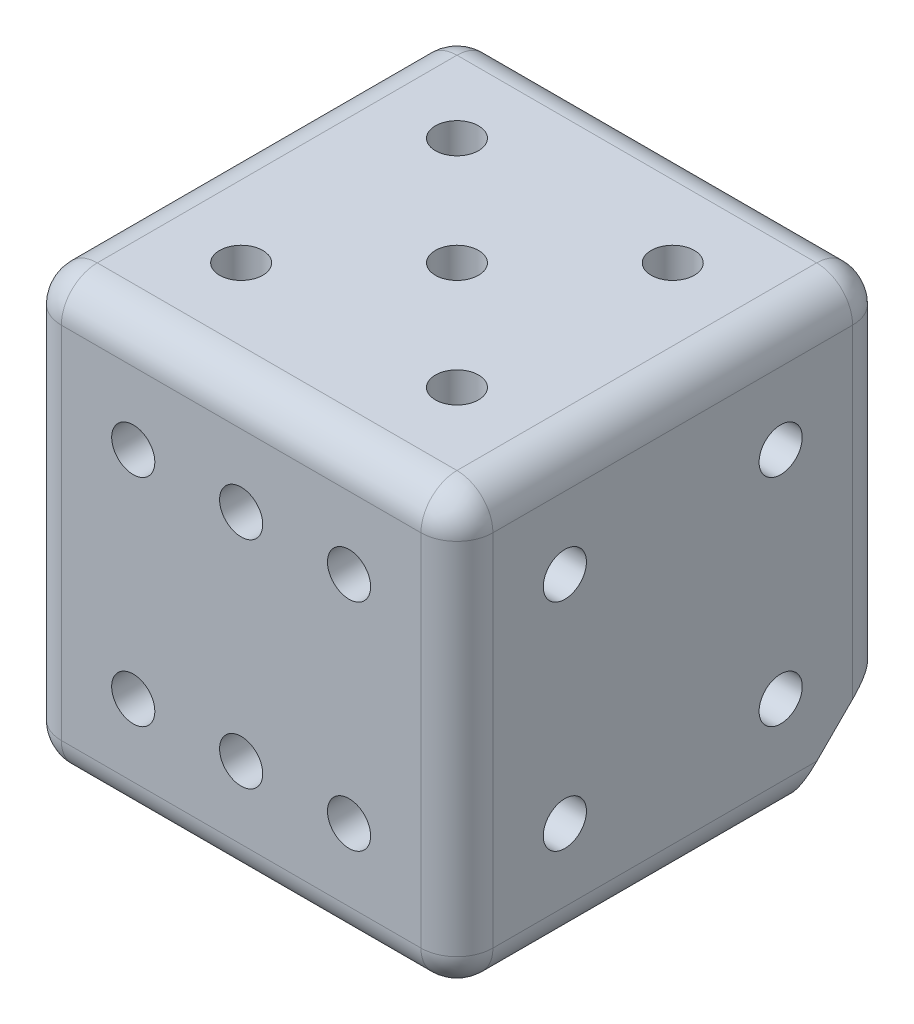
SolidWorks part; units mm, degrees
ref_plane "Ebene vorne" through (0, 0, 0) normal (0, 0, 1) x (1, 0, 0)
ref_plane "Ebene oben" through (0, 0, 0) normal (0, 1, 0) x (1, 0, 0)
ref_plane "Ebene rechts" through (0, 0, 0) normal (1, 0, 0) x (0, 0, -1)
sketch "Sketch1" plane through (0, 0, 0) normal (0, 1, 0) x (1, 0, 0)
  line L1 (0, 0) -> (30, 0)
  line L2 (0, 0) -> (0, 30)
  line L3 (0, 30) -> (30, 30)
  line L4 (30, 0) -> (30, 30)
  dimension "D1" = 30
  dimension "D2" = 30
extrude "Boss-Extrude1" add sketch "Sketch1" along normal blind 30
sketch "Sketch2" plane through (0, 0, 0) normal (0, 0, 1) x (1, 0, 0)
  line L0 (0, 30) -> (30, 30) construction
  line L1 (0, 30) -> (0, 0) construction
  point P0 (7.5, 22.5)
  point P7 (15, 22.5)
  point P8 (22.5, 22.5)
  point P9 (15, 7.5)
  point P10 (22.5, 7.5)
  point P11 (7.5, 7.5)
  dimension "D1" = 7.5
  dimension "D2" = 7.5
  dimension "D3" = 3
  dimension "D4" = 2
hole_wizard "Ø3.0 (3) Diameter Hole1" positions "3DSketch1" profile "Sketch3" hole size "Ø3.0" standard "ISO"
sketch3d "3DSketch1"
  point P0 (7.5, 22.5, 0)
  point P3 (15, 22.5, 0)
  point P6 (22.5, 22.5, 0)
  point P9 (22.5, 7.5, 0)
  point P12 (15, 7.5, 0)
  point P15 (7.5, 7.5, 0)
sketch "Sketch3" plane through (7.5, 22.5, 0) normal (1, 0, 0) x (0, -1, 0)
  line L0 (0, 0) -> (0, 3.4013)
  line L1 (0, 3.4013) -> (1.5, 2.5)
  line L2 (1.5, 2.5) -> (1.5, 0)
  line L5 (1.5, 0) -> (0, 0)
  line L10 (0, 3.4013) -> (-1.5, 2.5) construction
  line L11 (0, -6.35) -> (0, 107.95) construction
  dimension "Hole Dia." = 3
  dimension "Hole Depth" = 2.5
  dimension "Drill Angle" = 118
sketch "Sketch4" plane through (0, 30, 0) normal (0, 1, 0) x (1, 0, 0)
  line L0 (0, 30) -> (0, 0) construction
  line L1 (30, 30) -> (0, 30) construction
  point P0 (15, 15)
  point P5 (7.5, 22.5)
  point P8 (22.5, 22.5)
  point P9 (22.5, 7.5)
  point P10 (7.5, 7.5)
  dimension "D1" = 15
  dimension "D2" = 15
  dimension "D3" = 7.5
  dimension "D4" = 7.5
  dimension "D5" = 2
  dimension "D6" = 2
hole_wizard "Ø3.0 (3) Diameter Hole2" positions "3DSketch2" profile "Sketch5" hole size "Ø3.0" standard "ISO"
sketch3d "3DSketch2"
  point P0 (7.5, 30, -22.5)
  point P3 (15, 30, -15)
  point P6 (22.5, 30, -22.5)
  point P9 (22.5, 30, -7.5)
  point P12 (7.5, 30, -7.5)
sketch "Sketch5" plane through (7.5, 30, -22.5) normal (1, 0, 0) x (0, 0, 1)
  line L0 (0, 0) -> (0, 3.4013)
  line L1 (0, 3.4013) -> (1.5, 2.5)
  line L2 (1.5, 2.5) -> (1.5, 0)
  line L5 (1.5, 0) -> (0, 0)
  line L10 (0, 3.4013) -> (-1.5, 2.5) construction
  line L11 (0, -6.35) -> (0, 107.95) construction
  dimension "Hole Dia." = 3
  dimension "Hole Depth" = 2.5
  dimension "Drill Angle" = 118
sketch "Sketch6" plane through (0, 0, -30) normal (0, 0, -1) x (-1, 0, 0)
  line L0 (-30, 30) -> (-30, 0) construction
  line L1 (-30, 30) -> (0, 30) construction
  point P0 (-15, 15)
  dimension "D1" = 15
  dimension "D2" = 15
hole_wizard "Ø3.0 (3) Diameter Hole3" positions "3DSketch3" profile "Sketch7" hole size "Ø3.0" standard "ISO"
sketch3d "3DSketch3"
  point P0 (15, 15, -30)
sketch "Sketch7" plane through (15, 15, -30) normal (1, 0, 0) x (0, 1, 0)
  line L0 (0, 0) -> (0, 3.4013)
  line L1 (0, 3.4013) -> (1.5, 2.5)
  line L2 (1.5, 2.5) -> (1.5, 0)
  line L5 (1.5, 0) -> (0, 0)
  line L10 (0, 3.4013) -> (-1.5, 2.5) construction
  line L11 (0, -6.35) -> (0, 107.95) construction
  dimension "Hole Dia." = 3
  dimension "Hole Depth" = 2.5
  dimension "Drill Angle" = 118
sketch "Sketch8" plane through (0, 0, 0) normal (0, -1, 0) x (1, 0, 0)
  line L0 (0, 0) -> (30, 0) construction
  line L1 (0, -30) -> (0, 0) construction
  line L2 (30, -30) -> (0, -30) construction
  line L3 (30, 0) -> (30, -30) construction
  point P0 (7.5, -7.5)
  point P1 (22.5, -22.5)
  dimension "D1" = 7.5
  dimension "D2" = 7.5
  dimension "D3" = 7.5
  dimension "D4" = 7.5
hole_wizard "Ø3.0 (3) Diameter Hole4" positions "3DSketch4" profile "Sketch9" hole size "Ø3.0" standard "ISO"
sketch3d "3DSketch4"
  point P0 (7.5, 0, -7.5)
  point P3 (22.5, 0, -22.5)
sketch "Sketch9" plane through (7.5, 0, -7.5) normal (1, 0, 0) x (0, 0, -1)
  line L0 (0, 0) -> (0, 3.4013)
  line L1 (0, 3.4013) -> (1.5, 2.5)
  line L2 (1.5, 2.5) -> (1.5, 0)
  line L5 (1.5, 0) -> (0, 0)
  line L10 (0, 3.4013) -> (-1.5, 2.5) construction
  line L11 (0, -6.35) -> (0, 107.95) construction
  dimension "Hole Dia." = 3
  dimension "Hole Depth" = 2.5
  dimension "Drill Angle" = 118
sketch "Sketch10" plane through (30, 0, 0) normal (1, 0, 0) x (0, 0, -1)
  line L0 (0, 30) -> (0, 0) construction
  line L1 (0, 0) -> (30, 0) construction
  point P0 (7.5, 7.5)
  point P7 (7.5, 22.5)
  point P8 (22.5, 22.5)
  point P9 (22.5, 7.5)
  dimension "D1" = 7.5
  dimension "D2" = 7.5
  dimension "D3" = 2
  dimension "D4" = 2
hole_wizard "Ø3.0 (3) Diameter Hole5" positions "3DSketch5" profile "Sketch11" hole size "Ø3.0" standard "ISO"
sketch3d "3DSketch5"
  point P0 (30, 7.5, -7.5)
  point P3 (30, 7.5, -22.5)
  point P6 (30, 22.5, -22.5)
  point P9 (30, 22.5, -7.5)
sketch "Sketch11" plane through (30, 7.5, -7.5) normal (0, 1, 0) x (0, 0, -1)
  line L0 (0, 0) -> (0, 3.4013)
  line L1 (0, 3.4013) -> (1.5, 2.5)
  line L2 (1.5, 2.5) -> (1.5, 0)
  line L5 (1.5, 0) -> (0, 0)
  line L10 (0, 3.4013) -> (-1.5, 2.5) construction
  line L11 (0, -6.35) -> (0, 107.95) construction
  dimension "Hole Dia." = 3
  dimension "Hole Depth" = 2.5
  dimension "Drill Angle" = 118
sketch "Sketch12" plane through (0, 0, 0) normal (-1, 0, 0) x (0, 0, 1)
  line L0 (-30, 30) -> (0, 30) construction
  line L1 (0, 30) -> (0, 0) construction
  line L2 (-30, 30) -> (-30, 0) construction
  line L3 (-30, 0) -> (0, 0) construction
  point P0 (-7.5, 22.5)
  point P1 (-15, 15)
  point P2 (-22.5, 7.5)
  dimension "D1" = 7.5
  dimension "D2" = 7.5
  dimension "D3" = 15
  dimension "D4" = 15
  dimension "D5" = 7.5
  dimension "D6" = 7.5
hole_wizard "Ø3.0 (3) Diameter Hole6" positions "3DSketch6" profile "Sketch13" hole size "Ø3.0" standard "ISO"
sketch3d "3DSketch6"
  point P0 (0, 22.5, -7.5)
  point P3 (0, 15, -15)
  point P6 (0, 7.5, -22.5)
sketch "Sketch13" plane through (0, 22.5, -7.5) normal (0, 1, 0) x (0, 0, 1)
  line L0 (0, 0) -> (0, 3.4013)
  line L1 (0, 3.4013) -> (1.5, 2.5)
  line L2 (1.5, 2.5) -> (1.5, 0)
  line L5 (1.5, 0) -> (0, 0)
  line L10 (0, 3.4013) -> (-1.5, 2.5) construction
  line L11 (0, -6.35) -> (0, 107.95) construction
  dimension "Hole Dia." = 3
  dimension "Hole Depth" = 2.5
  dimension "Drill Angle" = 118
ref_plane "Plane1" through (10, -10, -10) normal (-0.5774, 0.5774, 0.5774) x (0.8165, 0.4082, 0.4082)
ref_plane "Plane2" through (17.5056, -17.5056, -17.5056) normal (-0.5774, 0.5774, 0.5774) x (0.8165, 0.4082, 0.4082)
sketch "Sketch14" plane through (17.5056, -17.5056, -17.5056) normal (-0.5774, 0.5774, 0.5774) x (0.8165, 0.4082, 0.4082)
  line L1 (2.9449, 13.5811) -> (20.7811, 13.5811)
  line L2 (2.9449, 13.5811) -> (2.9449, 28.3537)
  line L3 (2.9449, 28.3537) -> (20.7811, 28.3537)
  line L4 (20.7811, 13.5811) -> (20.7811, 28.3537)
extrude "Cut-Extrude1" cut sketch "Sketch14" against normal through all
fillet "Fillet1" radius 2.5 12 edges at (30, 0, -11.2583) (11.2583, 0, -30) (0, 0, -15) (15, 0, 0) (30, 18.7417, -30) (30, 15, 0) (30, 30, -15) (15, 30, 0) (0, 15, 0) (15, 30, -30) (0, 15, -30) (0, 30, -15)
